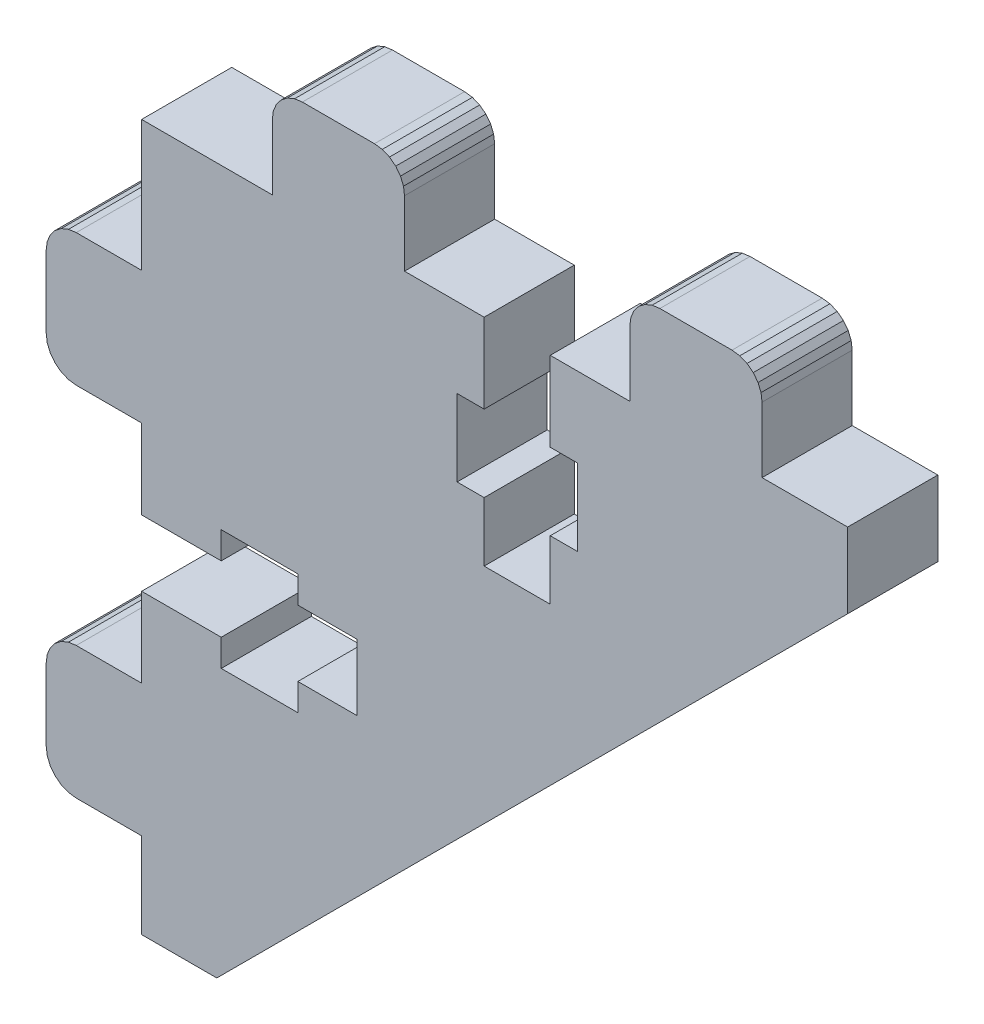
SolidWorks part; units mm, degrees
ref_plane "Plano frontal" through (0, 0, 0) normal (0, 0, 1) x (1, 0, 0)
ref_plane "Plano superior" through (0, 0, 0) normal (0, 1, 0) x (1, 0, 0)
ref_plane "Plano direito" through (0, 0, 0) normal (1, 0, 0) x (0, 0, -1)
sketch "Model" plane through (0, 0, 0) normal (0, 0, 1) x (1, 0, 0)
  line L0 (37.9693, 43.9962) -> (41.9193, 43.9962)
  line L1 (54.7693, 52.4462) -> (50.3693, 52.4462)
  line L2 (50.3693, 61.4962) -> (50.3693, 66.7962)
  line L3 (45.0693, 66.7962) -> (45.0693, 71.1462)
  line L4 (37.9693, 39.5962) -> (37.9693, 37.7962)
  line L5 (27.5693, 34.2962) -> (23.2193, 34.2962)
  line L6 (32.8693, 43.9962) -> (32.8693, 45.7962)
  line L7 (27.5693, 66.7962) -> (36.2693, 66.7962)
  line L8 (50.3693, 52.4462) -> (50.3693, 56.3962)
  line L9 (27.5693, 19.8032) -> (32.5733, 19.8032)
  line L10 (54.7693, 66.7962) -> (54.7693, 61.4962)
  line L11 (37.9693, 37.7962) -> (32.8693, 37.7962)
  line L12 (41.9193, 43.9962) -> (41.9193, 39.5962)
  line L13 (50.3693, 66.7962) -> (45.0693, 66.7962)
  line L14 (50.3693, 56.3962) -> (48.5693, 56.3962)
  line L15 (56.5693, 56.3962) -> (54.7693, 56.3962)
  line L16 (37.9693, 45.7962) -> (37.9693, 43.9962)
  line L17 (27.5693, 43.9962) -> (32.8693, 43.9962)
  line L18 (27.5693, 58.0962) -> (27.5693, 66.7962)
  line L19 (56.5693, 61.4962) -> (56.5693, 56.3962)
  line L20 (32.8693, 45.7962) -> (37.9693, 45.7962)
  line L21 (27.5693, 49.2962) -> (27.5693, 43.9962)
  line L22 (27.5693, 58.0962) -> (23.2193, 58.0962)
  line L23 (48.5693, 61.4962) -> (50.3693, 61.4962)
  line L24 (41.9193, 39.5962) -> (37.9693, 39.5962)
  line L25 (32.8693, 37.7962) -> (32.8693, 39.5962)
  line L26 (68.8693, 66.7962) -> (74.5664, 66.7962)
  line L27 (32.8693, 39.5962) -> (27.5693, 39.5962)
  line L28 (54.7693, 61.4962) -> (56.5693, 61.4962)
  line L29 (54.7693, 56.3962) -> (54.7693, 52.4462)
  line L30 (68.8693, 66.7962) -> (68.8693, 71.1462)
  line L31 (27.5693, 39.5962) -> (27.5693, 34.2962)
  line L32 (74.5664, 66.7962) -> (74.5664, 61.7949)
  line L33 (48.5693, 56.3962) -> (48.5693, 61.4962)
  line L34 (60.0693, 66.7962) -> (54.7693, 66.7962)
  line L35 (21.2193, 56.0962) -> (21.2193, 51.2962)
  line L36 (21.2193, 56.0962) -> (21.2874, 56.6138)
  line L37 (21.2874, 56.6138) -> (21.4872, 57.0962)
  line L38 (21.4872, 57.0962) -> (21.8051, 57.5104)
  line L39 (21.8051, 57.5104) -> (22.2193, 57.8282)
  line L40 (22.2193, 57.8282) -> (22.7017, 58.028)
  line L41 (22.7017, 58.028) -> (23.2193, 58.0962)
  line L42 (36.2693, 71.1462) -> (36.2693, 66.7962)
  line L43 (36.2693, 71.1462) -> (36.3374, 71.6638)
  line L44 (36.3374, 71.6638) -> (36.5372, 72.1462)
  line L45 (36.5372, 72.1462) -> (36.8551, 72.5604)
  line L46 (36.8551, 72.5604) -> (37.2693, 72.8782)
  line L47 (37.2693, 72.8782) -> (37.7516, 73.078)
  line L48 (37.7516, 73.078) -> (38.2693, 73.1462)
  line L49 (45.0693, 71.1462) -> (45.0011, 71.6638)
  line L50 (45.0011, 71.6638) -> (44.8013, 72.1462)
  line L51 (44.8013, 72.1462) -> (44.4835, 72.5604)
  line L52 (44.4835, 72.5604) -> (44.0693, 72.8782)
  line L53 (44.0693, 72.8782) -> (43.5869, 73.078)
  line L54 (43.0693, 73.1462) -> (38.2693, 73.1462)
  line L55 (43.5869, 73.078) -> (43.0693, 73.1462)
  line L56 (21.2193, 32.2962) -> (21.2193, 27.4962)
  line L57 (21.2193, 32.2962) -> (21.2874, 32.8138)
  line L58 (21.2874, 32.8138) -> (21.4872, 33.2962)
  line L59 (21.4872, 33.2962) -> (21.8051, 33.7104)
  line L60 (21.8051, 33.7104) -> (22.2193, 34.0283)
  line L61 (22.2193, 34.0283) -> (22.7017, 34.2281)
  line L62 (22.7017, 34.2281) -> (23.2193, 34.2962)
  line L63 (23.2193, 25.4962) -> (27.5693, 25.4962)
  line L64 (23.2193, 25.4962) -> (22.7017, 25.5644)
  line L65 (22.7017, 25.5644) -> (22.2193, 25.7642)
  line L66 (22.2193, 25.7642) -> (21.8051, 26.082)
  line L67 (21.8051, 26.082) -> (21.4872, 26.4962)
  line L68 (21.4872, 26.4962) -> (21.2874, 26.9786)
  line L69 (21.2874, 26.9786) -> (21.2193, 27.4962)
  line L70 (21.2193, 51.2962) -> (21.2874, 50.7786)
  line L71 (21.2874, 50.7786) -> (21.4872, 50.2962)
  line L72 (21.4872, 50.2962) -> (21.8051, 49.882)
  line L73 (21.8051, 49.882) -> (22.2193, 49.5642)
  line L74 (22.2193, 49.5642) -> (22.7017, 49.3643)
  line L75 (23.2193, 49.2962) -> (27.5693, 49.2962)
  line L76 (22.7017, 49.3643) -> (23.2193, 49.2962)
  line L77 (66.8693, 73.1462) -> (62.0693, 73.1462)
  line L78 (66.8693, 73.1462) -> (67.3869, 73.078)
  line L79 (67.3869, 73.078) -> (67.8693, 72.8782)
  line L80 (67.8693, 72.8782) -> (68.2835, 72.5604)
  line L81 (68.2835, 72.5604) -> (68.6013, 72.1462)
  line L82 (68.6013, 72.1462) -> (68.8011, 71.6638)
  line L83 (68.8011, 71.6638) -> (68.8693, 71.1462)
  line L84 (60.0693, 71.1462) -> (60.0693, 66.7962)
  line L85 (60.0693, 71.1462) -> (60.1374, 71.6638)
  line L86 (60.1374, 71.6638) -> (60.3372, 72.1462)
  line L87 (60.3372, 72.1462) -> (60.6551, 72.5604)
  line L88 (60.6551, 72.5604) -> (61.0693, 72.8782)
  line L89 (61.0693, 72.8782) -> (61.5516, 73.078)
  line L90 (61.5516, 73.078) -> (62.0693, 73.1462)
  line L91 (27.5693, 19.8032) -> (27.5693, 25.4962)
  line L92 (32.5733, 19.8032) -> (74.5664, 61.7949)
extrude "Ressalto-extrusão1" add sketch "Model" along normal blind 6
ref_plane "Plano1" through (52.5693, 0, 0) normal (-1, 0, 0) x (0, 0, 1)
ref_plane "Plano2" through (0, 41.7962, 0) normal (0, -1, 0) x (-1, 0, 0)
ref_plane "Plano3" through (0, 0, 3) normal (0, 0, 1) x (1, 0, 0)
